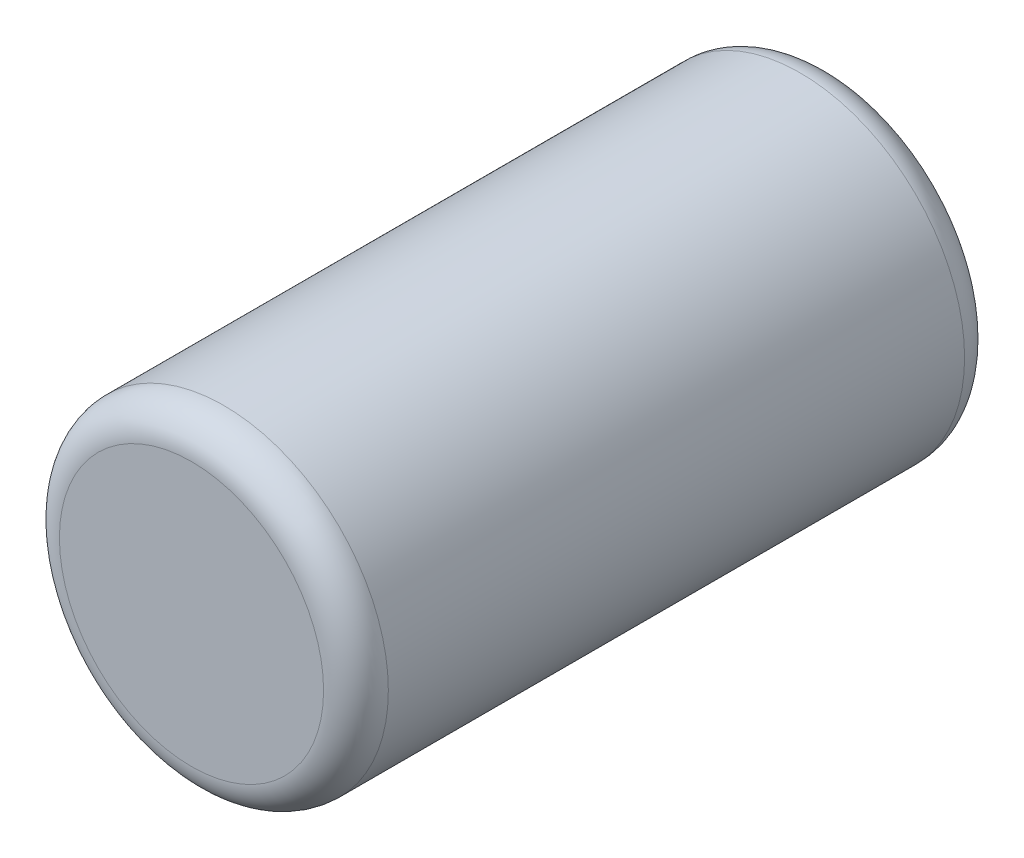
SolidWorks part; units mm, degrees
ref_plane "Front Plane" through (0, 0, 0) normal (0, 0, 1) x (1, 0, 0)
ref_plane "Top Plane" through (0, 0, 0) normal (0, 1, 0) x (1, 0, 0)
ref_plane "Right Plane" through (0, 0, 0) normal (1, 0, 0) x (0, 0, -1)
sketch "Sketch1" plane through (0, 0, 0) normal (0, 0, 1) x (1, 0, 0)
  circle A0 centre (0, 0) radius 25.4
  dimension "D1" = 50.8
extrude "Boss-Extrude1" add sketch "Sketch1" along normal blind 99
fillet "Fillet1" radius 5 2 edges at (25.4, 0, 99) (25.4, 0, 0)
